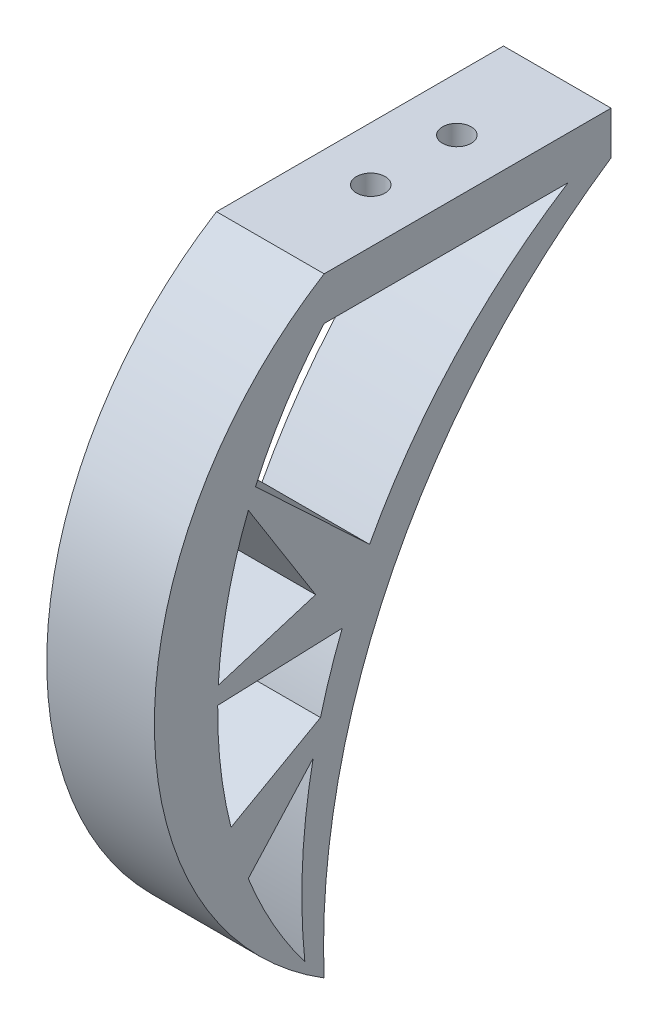
SolidWorks part; units mm, degrees
ref_plane "Front Plane" through (0, 0, 0) normal (0, 0, 1) x (1, 0, 0)
ref_plane "Top Plane" through (0, 0, 0) normal (0, 1, 0) x (1, 0, 0)
ref_plane "Right Plane" through (0, 0, 0) normal (1, 0, 0) x (0, 0, -1)
sketch "Sketch1" plane through (0, 0, 0) normal (0, 1, 0) x (1, 0, 0)
  line L1 (0, 0) -> (15, 0)
  line L2 (0, 0) -> (0, 40)
  line L3 (0, 40) -> (15, 40)
  line L4 (15, 0) -> (15, 40)
  dimension "D1" = 40
  dimension "D2" = 15
extrude "Boss-Extrude1" add sketch "Sketch1" along normal blind 6
sketch "Sketch2" plane through (0, 0, 0) normal (-1, 0, 0) x (0, 0, 1)
  line L0 (0, 6) -> (0, -79) construction
  line L1 (-40, 0) -> (0, -79) construction
  line L3 (0, 0) -> (0, 6)
  arc A0 (0, -79) -> (0, 6) centre (-26.3391, -36.5) ccw
  arc A1 (0, -79) -> (0, 0) centre (-45.1636, -39.5) ccw
  dimension "D2" = 50
  dimension "D3" = 60
  dimension "D1" = 85
extrude "Boss-Extrude3" add sketch "Sketch2" against normal blind 15
sketch "Sketch4" plane through (0, 0, 0) normal (-1, 0, 0) x (0, 0, 1)
  line L0 (-40, 0) -> (0, 0) construction
  line L1 (-34, 0) -> (-40, 0)
  line L5 (0, 6) -> (-40, 6)
  line L6 (-40, 6) -> (-40, 0)
  line L7 (-40, 0) -> (0, 0)
  line L8 (0, 6) -> (-40, 6)
  line L9 (-40, 6) -> (-40, 0)
  line L10 (-40, 0) -> (0, 0)
  arc A0 (0, -79) -> (-40, 0) centre (-90.5228, -75.2078) ccw
  arc A1 (2.5014, -77.3439) -> (-34, 0) centre (-76.8941, -67.5285) ccw
  arc A2 (0, -79) -> (0, 6) centre (-26.3391, -36.5) ccw construction
  arc A7 (0, -79) -> (0, 6) centre (-26.3391, -36.5) ccw
  arc A10 (0, -79) -> (0, 0) centre (-45.1636, -39.5) ccw
  arc A11 (2.5014, -77.3439) -> (0, 6) centre (-26.3391, -36.5) ccw
  arc A14 (0, -79) -> (0, 0) centre (-45.1636, -39.5) ccw
  line M5 (-40, 0) -> (0, 0)
  arc M7 (0, 0) -> (0, -79) centre (-45.1636, -39.5) cw
  dimension "D1" = 80
  dimension "D3" = 90.6022
  dimension "D2" = 3
  dimension "D4" = 6
  dimension "D5" = 0
extrude "Boss-Extrude7" add sketch "Sketch4" against normal blind 15 contours A1 A0 M7 M5
sketch "Sketch6" plane through (15, 0, 0) normal (1, 0, 0) x (0, 0, -1)
  line L0 (-23.5983, -39) -> (6.3361, -29.8248)
  line L1 (-23.5983, -39) -> (2.5289, -38.036)
  arc A0 (0, 6) -> (0, -79) centre (26.3391, -36.5) ccw construction
  arc A1 (34, 0) -> (-2.6877, -75.6974) centre (76.8941, -67.5285) ccw construction
  arc A2 (6.3361, -29.8248) -> (2.5289, -38.036) centre (2.5037, -33.0361) cw
  dimension "D2" = 5
  dimension "D1" = 31.309
  dimension "D3" = 26.1272
  dimension "D4" = 40
extrude "Boss-Extrude9" add sketch "Sketch6" against normal blind 15
sketch "Sketch7" plane through (15, 0, 0) normal (1, 0, 0) x (0, 0, -1)
  line L0 (-12.9749, -54.3296) -> (5.4918, -43.927)
  line L1 (5.4918, -43.927) -> (-14.2122, -65.7505)
  line L2 (-14.2122, -65.7505) -> (-12.9749, -54.3296)
  arc A0 (-14.8308, -38.6765) -> (-2.6877, -75.6974) centre (45.1636, -39.5) ccw construction
  arc A1 (40, 0) -> (0, -79) centre (90.5228, -75.2078) ccw construction
  arc A2 (0, 6) -> (0, -79) centre (26.3391, -36.5) ccw construction
  dimension "D1" = 29.4026
  dimension "D2" = 21.1951
  dimension "D3" = 11.4877
extrude "Boss-Extrude10" add sketch "Sketch7" against normal blind 15
sketch "Sketch8" plane through (15, 0, 0) normal (1, 0, 0) x (0, 0, -1)
  line L0 (-15.5935, -9.2667) -> (6.3361, -29.8248)
  line L1 (6.3361, -29.8248) -> (2.5289, -38.036)
  line L2 (2.5289, -38.036) -> (-15.5935, -9.2667)
  arc A0 (0, 6) -> (0, -79) centre (26.3391, -36.5) ccw construction
  dimension "D1" = 30.059
extrude "Boss-Extrude11" add sketch "Sketch8" against normal blind 15
sketch "Sketch11" plane through (0, 6, 0) normal (0, 1, 0) x (1, 0, 0)
  line L0 (7.5, 40) -> (7.5, 0) construction
  line L1 (15, 40) -> (0, 40) construction
  line L2 (0, 0) -> (15, 0) construction
  circle A0 centre (7.5, 20) radius 2.5 construction
  circle A1 centre (7.5, 26) radius 2
  circle A2 centre (7.5, 14) radius 2
  point P12 (0, 0)
  dimension "D1" = 5
  dimension "D2" = 4
  dimension "D3" = 4
  dimension "D4" = 6
  dimension "D5" = 6
extrude "Cut-Extrude2" cut sketch "Sketch11" against normal up to next
